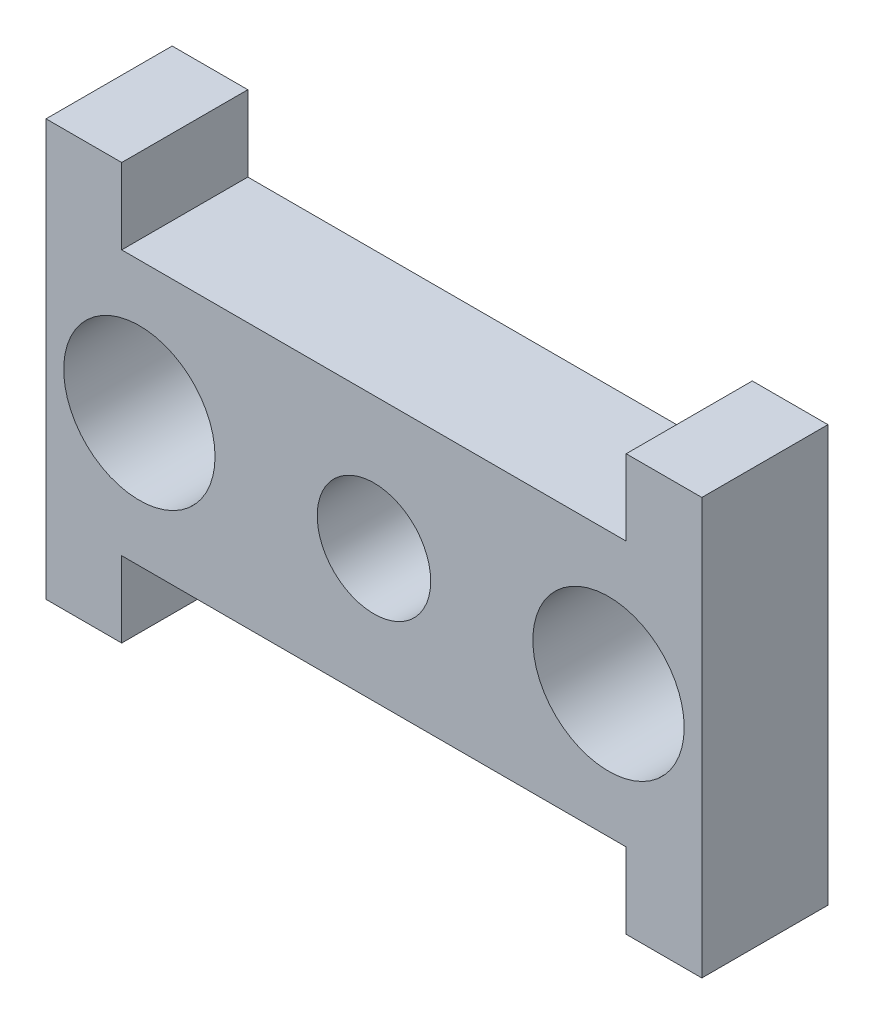
SolidWorks part; units mm, degrees
ref_plane "Front Plane" through (0, 0, 0) normal (0, 0, 1) x (1, 0, 0)
ref_plane "Top Plane" through (0, 0, 0) normal (0, 1, 0) x (1, 0, 0)
ref_plane "Right Plane" through (0, 0, 0) normal (1, 0, 0) x (0, 0, -1)
sketch "Sketch1" plane through (0, 0, 0) normal (0, 0, 1) x (1, 0, 0)
  line L0 (-13, 8.25) -> (13, -8.25) construction
  line L1 (-13, -8.25) -> (13, -8.25)
  line L2 (-13, -8.25) -> (-13, 8.25)
  line L3 (-13, 8.25) -> (13, 8.25)
  line L4 (13, -8.25) -> (13, 8.25)
  line L5 (-13, -8.25) -> (0, 0) construction
  line L6 (0, 0) -> (13, 8.25) construction
  line L7 (0, 0) -> (9.3, 0) construction
  line L8 (0, 8.25) -> (0, 0) construction
  line L9 (0, 0) -> (0, -8.25) construction
  line L10 (-10, 8.25) -> (-10, 5.25)
  line L11 (-10, 5.25) -> (10, 5.25)
  line L12 (10, 5.25) -> (10, 8.25)
  line L13 (-13, 5.25) -> (-10, 5.25) construction
  line L14 (10, 5.25) -> (13, 5.25) construction
  line L15 (10, -5.25) -> (10, -8.25)
  line L16 (-10, -8.25) -> (-10, -5.25)
  line L17 (-10, -5.25) -> (10, -5.25)
  line L18 (-10, 5.25) -> (-10, -5.25) construction
  circle A0 centre (0, 0) radius 2.25
  circle A1 centre (9.3, 0) radius 3
  circle A2 centre (-9.3, 0) radius 3
  dimension "D3" = 9.3
  dimension "D4" = 4.5
  dimension "D5" = 6
  dimension "D1" = 10.5
  dimension "D2" = 26
  dimension "D6" = 3
  dimension "D7" = 20
extrude "Boss-Extrude1" add sketch "Sketch1" along normal blind 5 contours L16 L17 L15 L1 L4 L3 L12 L11 L10 L2 A0 A1 A2
